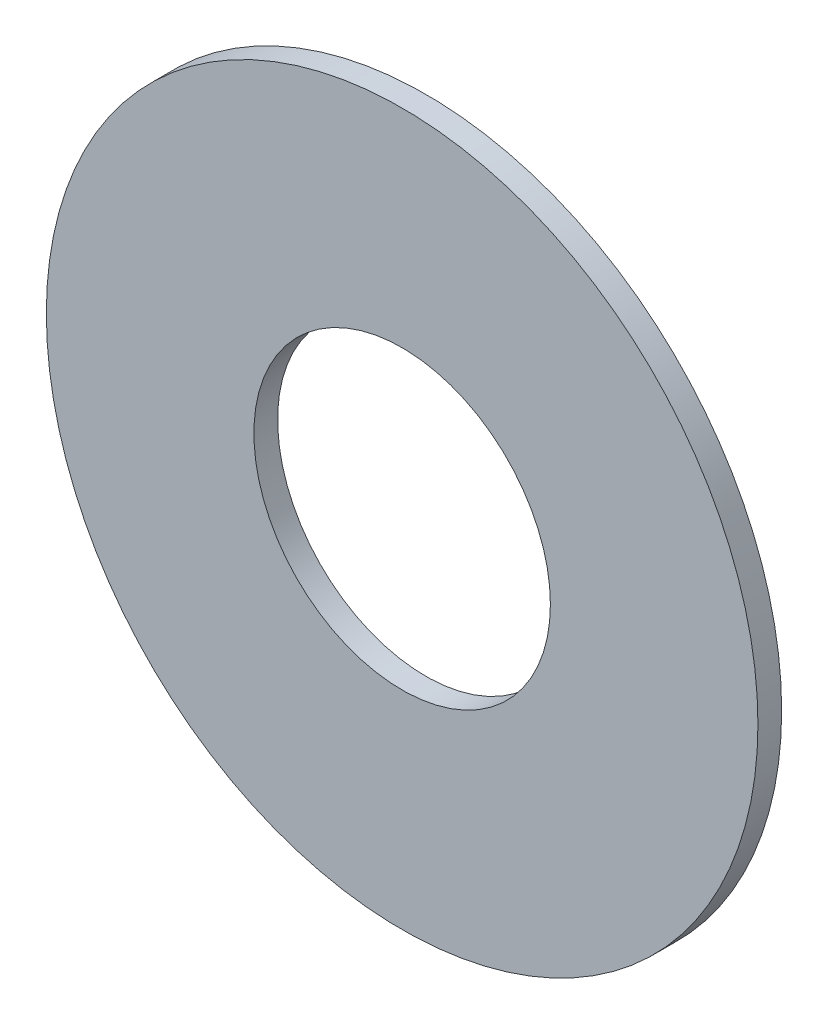
SolidWorks part; units mm, degrees
ref_plane "Front Plane" through (0, 0, 0) normal (0, 0, 1) x (1, 0, 0)
ref_plane "Top Plane" through (0, 0, 0) normal (0, 1, 0) x (1, 0, 0)
ref_plane "Right Plane" through (0, 0, 0) normal (1, 0, 0) x (0, 0, -1)
sketch "Sketch1" plane through (0, 0, 0) normal (0, 0, 1) x (1, 0, 0)
  circle A0 centre (0, 0) radius 79.375
  circle A1 centre (0, 0) radius 190.5
  dimension "D1" = 158.75
  dimension "D2" = 381
extrude "Boss-Extrude1" add sketch "Sketch1" along normal blind 12.7
sketch "Sketch2" plane through (0, 0, 0) normal (0, 0, -1) x (-1, 0, 0)
  line L0 (-190.5, 0) -> (190.5, 0) construction
  line L1 (0, -190.5) -> (0, 190.5) construction
  line L2 (-179.0114, 65.1548) -> (179.0114, -65.1548) construction
  line L3 (-179.0114, -65.1548) -> (179.0114, 65.1548) construction
  line L4 (-65.1548, 179.0114) -> (65.1548, -179.0114) construction
  line L5 (65.1548, 179.0114) -> (-65.1548, -179.0114) construction
  line L6 (-35.8352, 98.4563) -> (-11.967, 107.1436) construction
  line L7 (35.8786, 98.5756) -> (12.0104, 107.2629) construction
  line L8 (98.4563, 35.8352) -> (107.1436, 11.967) construction
  line L9 (98.5756, -35.8786) -> (107.2629, -12.0104) construction
  line L10 (35.8352, -98.4563) -> (11.967, -107.1436) construction
  line L11 (-35.8786, -98.5756) -> (-12.0104, -107.2629) construction
  line L12 (-98.4563, -35.8352) -> (-107.1436, -11.967) construction
  line L13 (-98.5756, 35.8786) -> (-107.2629, 12.0104) construction
  circle A0 centre (0, 0) radius 190.5 construction
  circle A1 centre (0, 0) radius 79.375 construction
  point P37 (0, 0)
  dimension "D1" = 20
  dimension "D2" = 20
  dimension "D3" = 20
  dimension "D4" = 20
  dimension "D5" = 104.775
  dimension "D6" = 25.4
  dimension "D7" = 104.902
  dimension "D8" = 25.4
  dimension "D9" = 4
